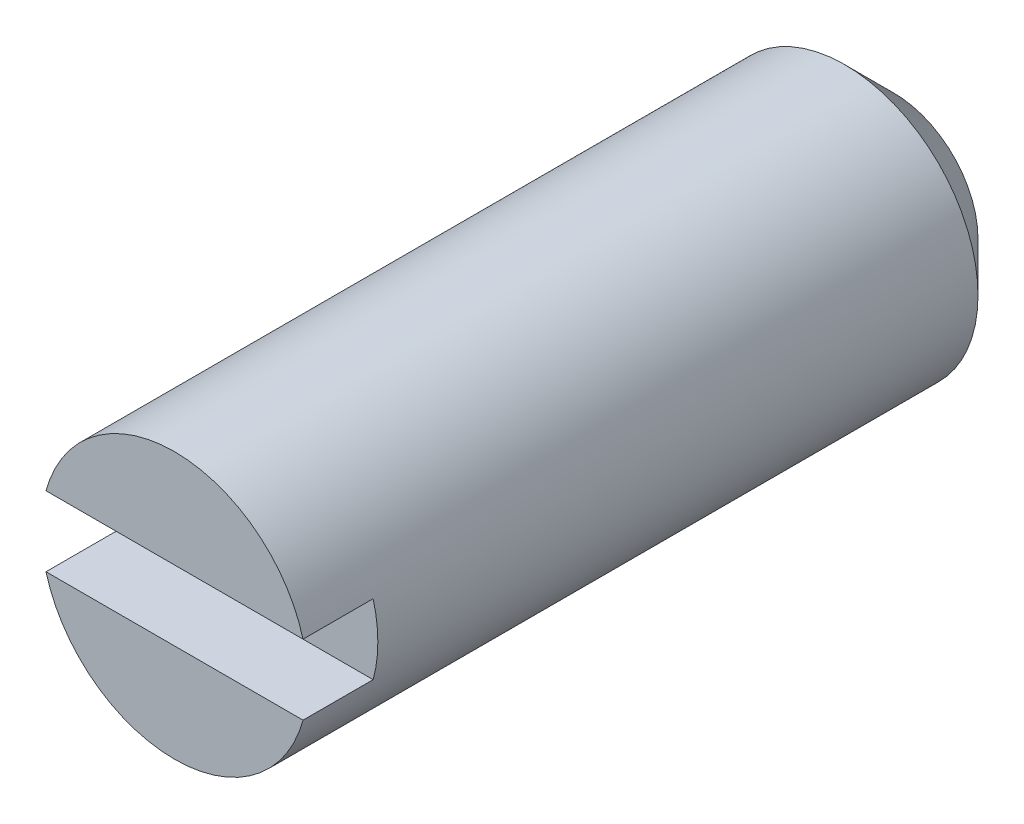
SolidWorks part; units mm, degrees
ref_plane "Front Plane" through (0, 0, 0) normal (0, 0, 1) x (1, 0, 0)
ref_plane "Top Plane" through (0, 0, 0) normal (0, 1, 0) x (1, 0, 0)
ref_plane "Right Plane" through (0, 0, 0) normal (1, 0, 0) x (0, 0, -1)
sketch "Sketch1" plane through (0, 0, 0) normal (0, 0, 1) x (1, 0, 0)
  circle A1 centre (6.35, 0) radius 2.413
  dimension "D1" = 4.826
extrude "Extrude1" add sketch "Sketch1" along normal blind 13.0302
chamfer "Chamfer1" distance 0.889 angle 45 1 edges at (8.763, 0, 0)
sketch "Sketch3" plane through (0, 0, 13.0302) normal (0, 0, 1) x (1, 0, 0)
  line L0 (3.937, -0.635) -> (8.763, 0.635) construction
  line L1 (3.937, 0.635) -> (8.763, 0.635)
  line L2 (3.937, 0.635) -> (3.937, -0.635)
  line L3 (3.937, -0.635) -> (8.763, -0.635)
  line L4 (8.763, 0.635) -> (8.763, -0.635)
  circle A0 centre (6.35, 0) radius 2.413 construction
  circle A1 centre (6.35, 0) radius 2.413 construction
  dimension "D1" = 1.27
extrude "Cut-Extrude1" cut sketch "Sketch3" against normal blind 1.27
sketch "Sketch4" plane through (0, 0, 0) normal (0, 1, 0) x (1, 0, 0)
  line L0 (6.35, 0) -> (6.35, -0.5588) construction
  line L1 (7.874, 0) -> (4.826, 0) construction
  line L2 (6.35, 0.635) -> (7.8239, 0.635) construction
  line L3 (6.35, 0.635) -> (6.35, -1.7526)
  circle A0 centre (6.35, -0.5588) radius 1.1938 construction
  arc A1 (6.35, 0.635) -> (6.35, -1.7526) centre (6.35, -0.5588) ccw
  dimension "D1" = 2.3876
  dimension "D2" = 0.635
revolve "Revolve3" add sketch "Sketch4" angle 360 about L3
